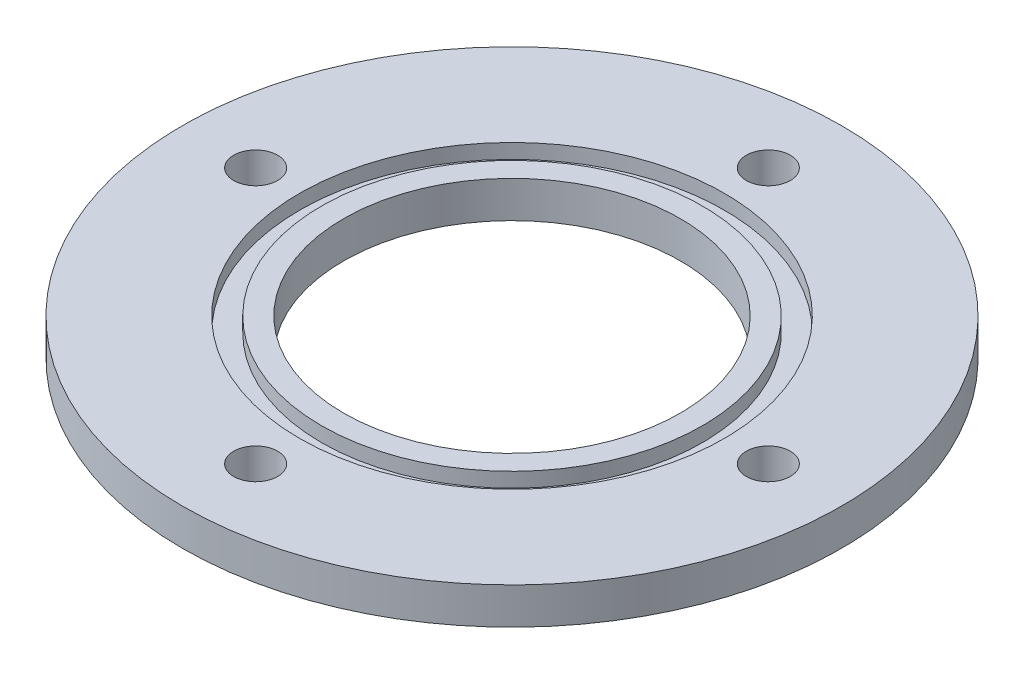
SolidWorks part; units mm, degrees
ref_plane "前基準面" through (0, 0, 0) normal (0, 0, 1) x (1, 0, 0)
ref_plane "上基準面" through (0, 0, 0) normal (0, 1, 0) x (1, 0, 0)
ref_plane "右基準面" through (0, 0, 0) normal (1, 0, 0) x (0, 0, -1)
sketch "草圖1" plane through (0, 0, 0) normal (0, 1, 0) x (1, 0, 0)
  line L0 (0, 0) -> (0, 75.702) construction
  line L1 (0, 75.702) -> (0, -85.4399) construction
  line L2 (0, 0) -> (137.2261, 0) construction
  line L3 (137.2261, 0) -> (-111.8072, 0) construction
  circle A0 centre (0, 0) radius 23
  circle A1 centre (0, 0) radius 45
  circle A2 centre (0, 35) radius 3
  circle A3 centre (0, -35) radius 3
  circle A4 centre (35, 0) radius 3
  circle A5 centre (-35, 0) radius 3
  dimension "D1" = 46
  dimension "D2" = 90
  dimension "D7" = 6
  dimension "D8" = 6
  dimension "D9" = 6
  dimension "D10" = 6
  dimension "D3" = 35
  dimension "D4" = 35
  dimension "37.5" = 35
  dimension "D6" = 35
extrude "填料-伸長3" add sketch "草圖1" along normal blind 5 contours A1 A5 A4 A3 A2 A0
sketch "Sketch1" plane through (0, 5, 0) normal (0, 1, 0) x (1, 0, 0)
  circle A0 centre (0, 0) radius 27.5 construction
  circle A1 centre (0, 0) radius 29
  circle A2 centre (0, 0) radius 26
  dimension "D1" = 55
  dimension "D2" = 3
  dimension "D3" = 1.5
extrude "Cut-Extrude1" cut sketch "Sketch1" against normal blind 2
